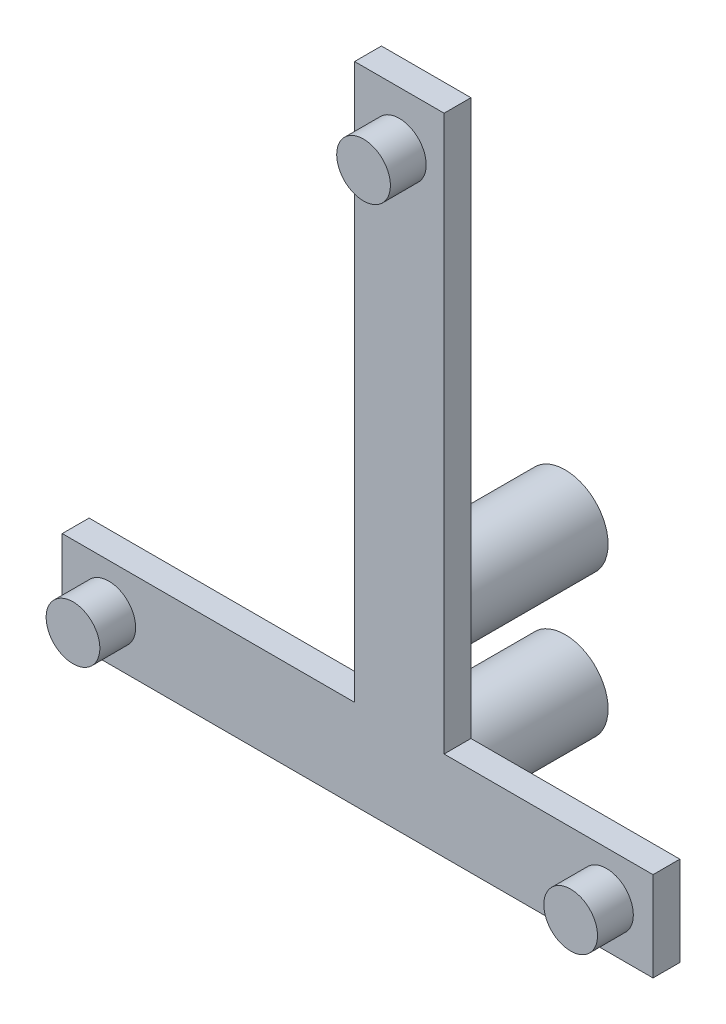
SolidWorks part; units mm, degrees
ref_plane "Front Plane" through (0, 0, 0) normal (0, 0, 1) x (1, 0, 0)
ref_plane "Top Plane" through (0, 0, 0) normal (0, 1, 0) x (1, 0, 0)
ref_plane "Right Plane" through (0, 0, 0) normal (1, 0, 0) x (0, 0, -1)
sketch "Sketch4" plane through (0, 0, 0) normal (0, 0, 1) x (1, 0, 0)
  line L0 (-139.5612, 16.0705) -> (-106.5612, 16.0705)
  line L1 (-106.5612, 16.0705) -> (-106.5612, 21.0705)
  line L2 (-106.5612, 21.0705) -> (-118.2312, 21.0705)
  line L3 (-118.2312, 21.0705) -> (-118.2312, 52.0705)
  line L4 (-118.2312, 52.0705) -> (-123.2312, 52.0705)
  line L5 (-123.2312, 52.0705) -> (-123.2312, 21.0705)
  line L6 (-123.2312, 21.0705) -> (-139.5612, 21.0705)
  line L7 (-139.5612, 21.0705) -> (-139.5612, 16.0705)
  dimension "D1" = 5
  dimension "D2" = 5
  dimension "D3" = 5
  dimension "D4" = 33
  dimension "D5" = 16.33
  dimension "D6" = 31
extrude "Boss-Extrude2" add sketch "Sketch4" along normal blind 1.5
sketch "Sketch5" plane through (0, 0, 0) normal (0, 0, -1) x (-1, 0, 0)
  line L0 (106.5612, 16.0705) -> (106.5612, 21.0705) construction
  line L1 (139.5612, 16.0705) -> (106.5612, 16.0705) construction
  line L2 (118.2312, 21.0705) -> (118.2312, 52.0705) construction
  circle A0 centre (136.9612, 18.5705) radius 1.5
  circle A1 centre (109.1612, 18.5705) radius 1.5
  circle A2 centre (120.7312, 49.0705) radius 1.5
  dimension "D1" = 27.8
  dimension "D2" = 3
  dimension "D3" = 3
  dimension "D4" = 2.6
  dimension "D5" = 2.5
  dimension "D6" = 2.5
  dimension "D7" = 3
  dimension "D8" = 30.5
  dimension "D9" = 2.5
extrude "Boss-Extrude5" add sketch "Sketch5" against normal blind 3.5
sketch "Sketch6" plane through (0, 0, 0) normal (0, 0, -1) x (-1, 0, 0)
  line L0 (139.5612, 16.0705) -> (106.5612, 16.0705) construction
  line L1 (118.2312, 21.0705) -> (118.2312, 52.0705) construction
  circle A0 centre (120.7312, 18.5705) radius 2.4
  circle A1 centre (120.7312, 26.5405) radius 2.4
  dimension "D1" = 4.8
  dimension "D2" = 4.8
  dimension "D3" = 2.5
  dimension "D4" = 2.5
  dimension "D5" = 2.5
  dimension "D6" = 7.97
extrude "Boss-Extrude6" add sketch "Sketch6" along normal blind 7.76
